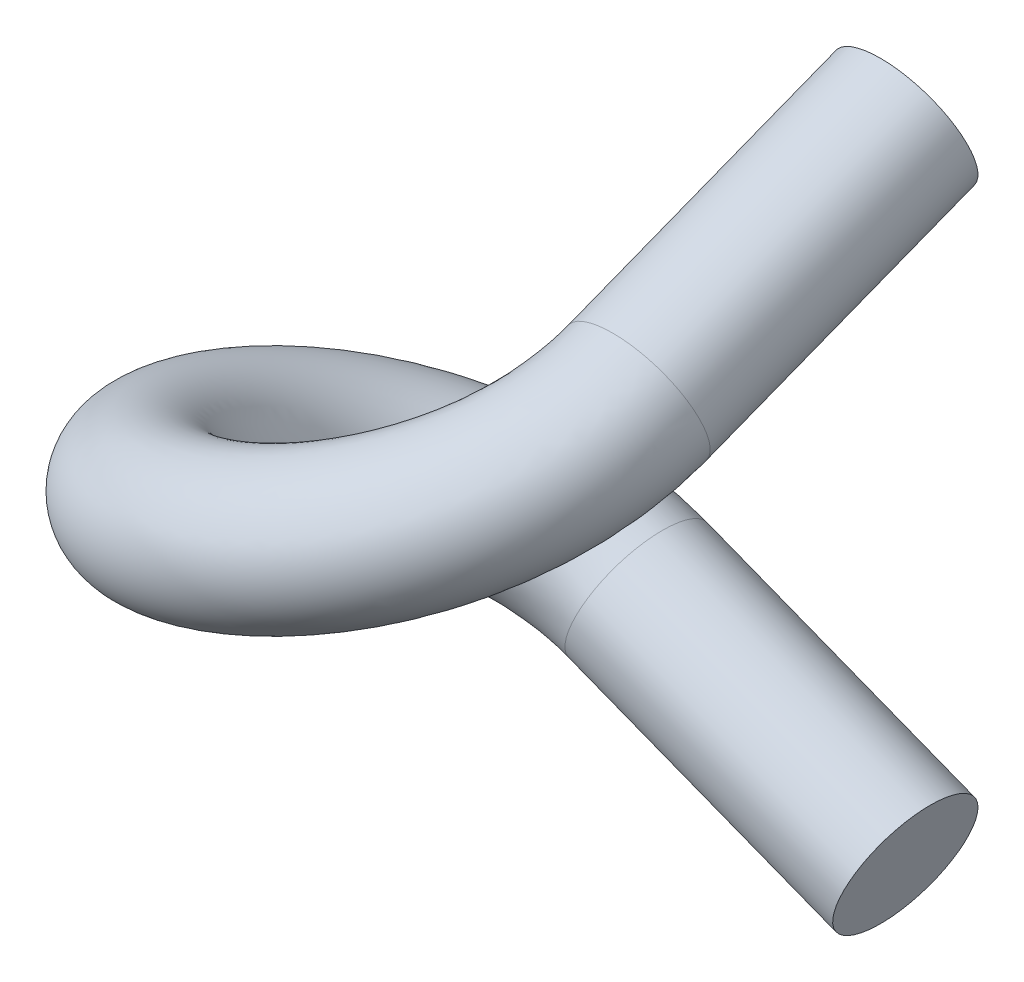
SolidWorks part; units mm, degrees
ref_plane "Ebene vorne" through (0, 0, 0) normal (0, 0, 1) x (1, 0, 0)
ref_plane "Ebene oben" through (0, 0, 0) normal (0, 1, 0) x (1, 0, 0)
ref_plane "Ebene rechts" through (0, 0, 0) normal (1, 0, 0) x (0, 0, -1)
sketch "Skizze2" plane through (0, 0, 0) normal (0, 1, 0) x (1, 0, 0)
  circle A0 centre (0, 0) radius 9
  point P0 (0, 0)
  dimension "D1" = 18
curve "Spirale/Helix1" pitch 22 height 16.5 turns 0.75
sketch3d "3D-Skizze1"
  line L0 (0, -16.5, -9) -> (11.7536, -21.0727, -9)
  line L1 (9, 0, 0) -> (9, 4.5727, -11.7536)
  spline S0 degree 3 poles (-1119.2472, -124.4993, 2768.4059) (-173.7117, 28.3759, -154.3888) (28.6523, 12.4298, -26.5384) (6.5296, -2.7497, 6.5288) (3.5338, -4.1251, 8.5316) (0, -5.5, 9.2342) (-3.5338, -6.875, 8.5314) (-6.5296, -8.25, 6.5296) (-8.5314, -9.625, 3.5338) (-9.2342, -11, 0) (-8.5316, -12.3749, -3.5338) (-6.5288, -13.7503, -6.5296) (26.538, -28.9296, -28.652) (154.3855, -44.8755, 173.7065) (-2768.2897, 107.9932, 1119.2096) knots -2.51292 -2.51292 -2.51292 -2.51292 0.083333 0.166667 0.25 0.333333 0.416667 0.5 0.583333 0.666667 0.75 0.833333 0.916667 3.512885 3.512885 3.512885 3.512885 only from (9, 0, 0) to (0, -16.5, -9) construction
  spline S1 degree 3 poles (9, 0, 0) (9, -0.4558, 1.1715) (8.5314, -1.3762, 3.5368) (6.5296, -2.7497, 6.5288) (3.5338, -4.1251, 8.5316) (0, -5.5, 9.2342) (-3.5338, -6.875, 8.5314) (-6.5296, -8.25, 6.5296) (-8.5314, -9.625, 3.5338) (-9.2342, -11, 0) (-8.5316, -12.3749, -3.5338) (-6.5288, -13.7503, -6.5296) (-3.5368, -15.1238, -8.5314) (-1.1715, -16.0442, -9) (0, -16.5, -9) knots 0 0 0 0 0.083333 0.166667 0.25 0.333333 0.416667 0.5 0.583333 0.666667 0.75 0.833333 0.916667 1 1 1 1
  point P4 (7.8229, 12.5501, -0.4079)
ref_plane "Ebene1" through (9, 4.5727, -11.7536) normal (0, 0.3626, -0.932) x (-1, 0, 0)
sketch "Skizze5" plane through (9, 4.5727, -11.7536) normal (0, 0.3626, -0.932) x (-1, 0, 0)
  circle A0 centre (0, 0) radius 3
  dimension "D1" = 6
sweep "Austragung1" add profiles "Skizze5" path "3D-Skizze1"
